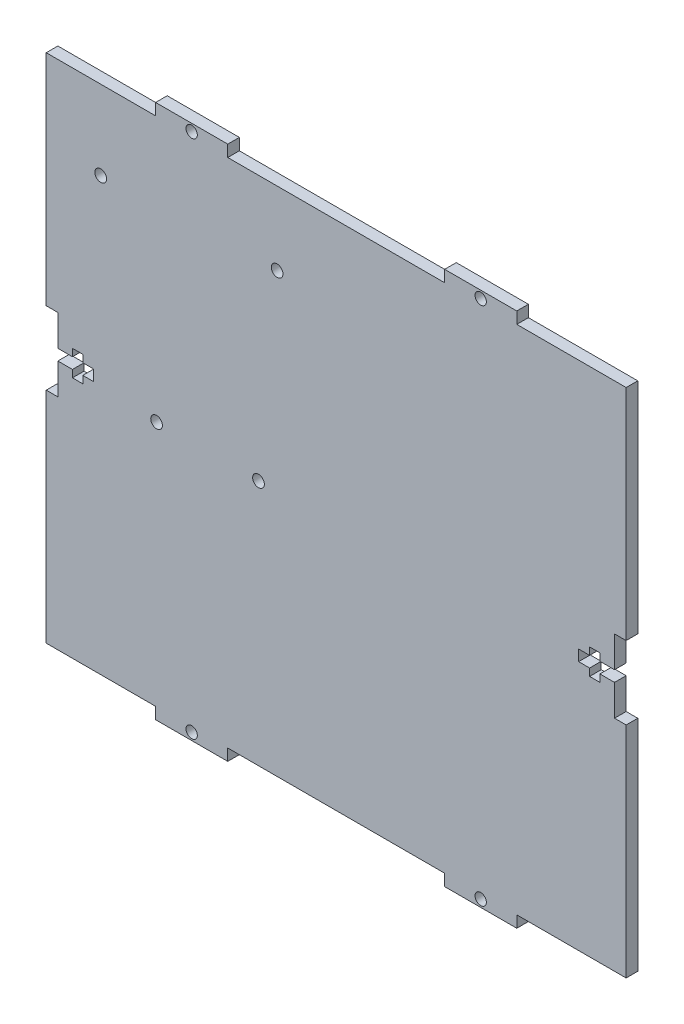
SolidWorks part; units mm, degrees
ref_plane "Front Plane" through (0, 0, 0) normal (0, 0, 1) x (1, 0, 0)
ref_plane "Top Plane" through (0, 0, 0) normal (0, 1, 0) x (1, 0, 0)
ref_plane "Right Plane" through (0, 0, 0) normal (1, 0, 0) x (0, 0, -1)
sketch "Sketch1" plane through (0, 0, 0) normal (0, 0, 1) x (1, 0, 0)
  line L0 (0, 0) -> (50000, 0) construction
  line L1 (-79.38, 73.18) -> (79.38, 73.18)
  line L2 (-79.38, 73.18) -> (-79.38, -73.18)
  line L3 (-79.38, -73.18) -> (79.38, -73.18)
  line L4 (79.38, 73.18) -> (79.38, -73.18)
  line L5 (0, 0) -> (0, 50000) construction
  point P0 (0, 0)
  dimension "D1" = 158.76
  dimension "D2" = 146.36
  dimension "D3" = 73.18
  dimension "D4" = 79.38
extrude "Boss-Extrude1" add sketch "Sketch1" along normal blind 3.18
sketch "Sketch2" plane through (0, 0, 3.18) normal (0, 0, 1) x (1, 0, 0)
  line L0 (79.38, 73.18) -> (-79.38, 73.18) construction
  line L1 (-79.38, 73.18) -> (-49.44, 73.18)
  line L2 (-79.38, 73.18) -> (-79.38, 70)
  line L3 (-79.38, 70) -> (-49.44, 70)
  line L4 (-49.44, 73.18) -> (-49.44, 70)
  line L5 (0, 0) -> (0, 36.9954) construction
  line L6 (-29.69, 73.18) -> (29.69, 73.18)
  line L7 (-29.69, 73.18) -> (-29.69, 70)
  line L8 (-29.69, 70) -> (29.69, 70)
  line L9 (29.69, 73.18) -> (29.69, 70)
  line L10 (79.38, 73.18) -> (49.44, 73.18)
  line L11 (79.38, 73.18) -> (79.38, 70)
  line L12 (79.38, 70) -> (49.44, 70)
  line L13 (49.44, 73.18) -> (49.44, 70)
  line L14 (0, 0) -> (50000, 0) construction
  dimension "D1" = 3.18
  dimension "D2" = 3.18
  dimension "D3" = 3.18
  dimension "D4" = 29.69
  dimension "D5" = 29.94
  dimension "D6" = 59.38
  dimension "D7" = 19.75
  dimension "D8" = 29.94
extrude "Cut-Extrude1" cut sketch "Sketch2" against normal through all both and the other way through all
mirror "Mirror1" about plane through (0, 0, 0) normal (0, 1, 0) of "Cut-Extrude1"
sketch "Sketch3" plane through (0, 0, 3.18) normal (0, 0, 1) x (1, 0, 0)
  line L0 (-49.44, -73.18) -> (-29.69, -73.18) construction
  circle A0 centre (-39.565, -71.18) radius 1.55
  dimension "D1" = 3.1
  dimension "D2" = 2
  dimension "D3" = 9.875
extrude "Cut-Extrude2" cut sketch "Sketch3" against normal through all both and the other way through all
mirror "Mirror2" about plane through (0, 0, 0) normal (1, 0, 0) of "Cut-Extrude2"
mirror "Mirror3" about plane through (0, 0, 0) normal (0, 1, 0) of "Mirror2", "Cut-Extrude2"
sketch "Sketch5" plane through (0, 0, 0) normal (0, 0, -1) x (-1, 0, 0)
  line L0 (0, 0) -> (50000, 0) construction
  line L1 (-79.38, -70) -> (-79.38, 70) construction
  line L2 (-79.38, -10) -> (-76.2, -10)
  line L3 (-79.38, -10) -> (-79.38, 10)
  line L4 (-79.38, 10) -> (-76.2, 10)
  line L5 (-76.2, -10) -> (-76.2, 10)
  line L7 (-72.2, 3.5) -> (-69.38, 3.5)
  line L8 (-79.38, 1.5) -> (-66.38, 1.5)
  line L9 (-79.38, 1.5) -> (-79.38, -1.5)
  line L10 (-79.38, -1.5) -> (-66.38, -1.5)
  line L11 (-66.38, 1.5) -> (-66.38, -1.5)
  line L12 (-72.2, 3.5) -> (-72.2, -3.5)
  line L13 (-72.2, -3.5) -> (-69.38, -3.5)
  line L14 (-69.38, 3.5) -> (-69.38, -3.5)
  point P9 (-76.2, 0)
  line M29 (-79.38, 70) -> (-79.38, -70)
  dimension "D1" = 0
  dimension "D2" = 20
  dimension "D3" = 3.18
  dimension "D4" = 9.82
  dimension "D5" = 3
  dimension "D6" = 1.5
  dimension "D7" = 4
  dimension "D8" = 3
  dimension "D9" = 7
  dimension "D10" = 3.5
extrude "Cut-Extrude3" cut sketch "Sketch5" against normal through all both and the other way through all contours L8 L5 L4 M29 | L3 L0 L5 L8 | L0 L9 L10 L5 | L10 L2 L5 M29 | L5 L0 L12 L8 | L0 L5 L10 L12 | L14 L7 L12 L8 | L12 L0 L14 L8 | L0 L12 L10 L14 | L14 L10 L12 L13 | L14 L0 L11 L8 | L0 L14 L10 L11
sketch "Sketch6" plane through (0, 0, 0) normal (0, 0, -1) x (-1, 0, 0)
  line L0 (0, 0) -> (0, 50000) construction
mirror "Mirror4" about plane through (0, 0, 0) normal (1, 0, 0) of "Cut-Extrude3"
sketch "Sketch7" plane through (0, 0, 0) normal (0, 0, -1) x (-1, 0, 0)
  circle A0 centre (64.4745, 48.325) radius 1.6
  circle A1 centre (16.1745, 49.925) radius 1.6
  circle A2 centre (49.1745, -2.475) radius 1.6
  circle A3 centre (21.2745, -2.475) radius 1.6
  dimension "D1" = 3.2
  dimension "D2" = 3.2
  dimension "D3" = 3.2
  dimension "D4" = 3.2
extrude "Cut-Extrude4" cut sketch "Sketch7" against normal through all both and the other way through all
